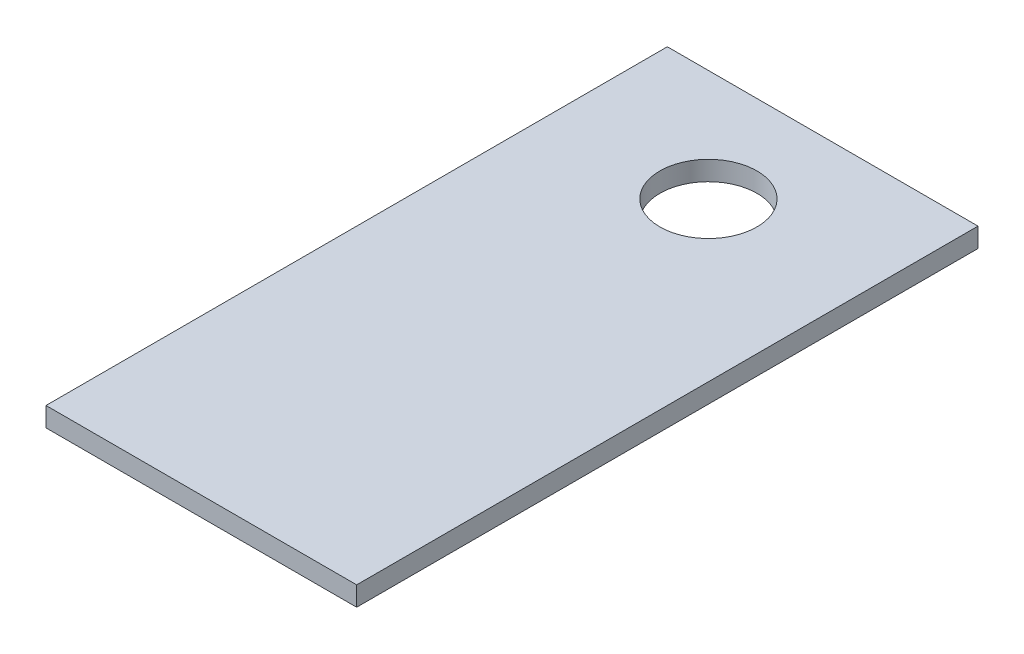
SolidWorks part; units mm, degrees
ref_plane "Front Plane" through (0, 0, 0) normal (0, 0, 1) x (1, 0, 0)
ref_plane "Top Plane" through (0, 0, 0) normal (0, 1, 0) x (1, 0, 0)
ref_plane "Right Plane" through (0, 0, 0) normal (1, 0, 0) x (0, 0, -1)
sketch "Sketch1" plane through (0, 0, 0) normal (0, 1, 0) x (1, 0, 0)
  line L1 (0, 0) -> (25.4, 0)
  line L2 (0, 0) -> (0, 50.8)
  line L3 (0, 50.8) -> (25.4, 50.8)
  line L4 (25.4, 0) -> (25.4, 50.8)
  circle A0 centre (12.4542, 41.7052) radius 3.9687
  dimension "D3" = 7.9375
  dimension "D1" = 25.4
  dimension "D2" = 50.8
extrude "Boss-Extrude1" add sketch "Sketch1" along normal blind 1.5875
equation "\"in\"=50.8"
